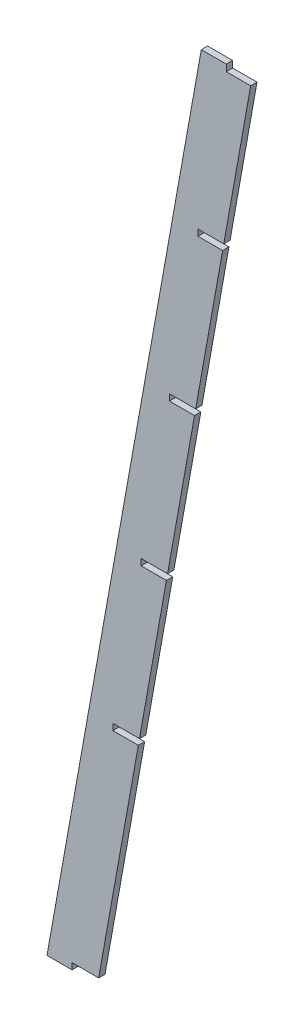
SolidWorks part; units mm, degrees
material "Plywood"
ref_plane "Front Plane" through (0, 0, 0) normal (0, 0, 1) x (1, 0, 0)
ref_plane "Top Plane" through (0, 0, 0) normal (0, 1, 0) x (1, 0, 0)
ref_plane "Right Plane" through (0, 0, 0) normal (1, 0, 0) x (0, 0, -1)
sketch "Sketch1" plane through (0, 0, 0) normal (0, 1, 0) x (1, 0, 0)
  line L1 (0, 0) -> (25.4, 0)
  line L2 (0, 0) -> (0, 3.175)
  line L3 (0, 3.175) -> (25.4, 3.175)
  line L4 (25.4, 0) -> (25.4, 3.175)
  dimension "D1" = 25.4
  dimension "D2" = 3.175
ref_plane "Plane1" through (0, 432.562, 0) normal (0, 1, 0) x (1, 0, 0)
sketch "Sketch2" plane through (0, 432.562, 0) normal (0, 1, 0) x (1, 0, 0)
  line L1 (77.47, 0) -> (102.87, 0)
  line L2 (77.47, 0) -> (77.47, 3.175)
  line L3 (77.47, 3.175) -> (102.87, 3.175)
  line L4 (102.87, 0) -> (102.87, 3.175)
  dimension "D1" = 25.4
  dimension "D2" = 3.175
  dimension "D3" = 0
  dimension "D4" = 77.47
loft "Loft1" add profiles "Sketch1", "Sketch2"
sketch "Sketch3" plane through (0, 0, 0) normal (0, 0, 1) x (1, 0, 0)
  line L0 (90.0287, 432.562) -> (90.0287, 429.26)
  line L9 (12.5729, 3.175) -> (12.5729, 0)
  line L11 (102.2786, 429.26) -> (90.0287, 429.26)
  line L12 (25.4, 0) -> (102.87, 432.562) construction
  line L13 (90.0287, 432.562) -> (102.87, 432.562)
  line L14 (102.87, 432.562) -> (102.2786, 429.26)
  line L15 (33.0714, 117.475) -> (33.0714, 114.3)
  line L16 (75.7597, 353.7381) -> (75.7597, 350.5952)
  line L17 (75.7597, 353.7381) -> (88.753, 353.7381)
  line L18 (75.7597, 350.5952) -> (88.1901, 350.5952)
  line L19 (88.1901, 350.5952) -> (88.753, 353.7381)
  line L20 (61.4709, 274.955) -> (61.4709, 271.78)
  line L21 (47.2604, 193.04) -> (47.2604, 196.215)
  line L22 (61.4709, 271.78) -> (74.0746, 271.78)
  line L23 (74.0746, 271.78) -> (74.6433, 274.955)
  line L24 (74.6433, 274.955) -> (61.4709, 274.955)
  line L25 (60.5413, 196.215) -> (59.9726, 193.04)
  line L26 (59.9726, 193.04) -> (47.2604, 193.04)
  line L27 (47.2604, 196.215) -> (60.5413, 196.215)
  line L28 (45.8706, 114.3) -> (46.4393, 117.475)
  line L29 (46.4393, 117.475) -> (33.0714, 117.475)
  line L30 (33.0714, 114.3) -> (45.8706, 114.3)
  line L31 (12.5729, 0) -> (25.4, 0)
  line L32 (25.4, 0) -> (25.9686, 3.175)
  line L33 (25.9686, 3.175) -> (12.5729, 3.175)
extrude "Cut-Extrude1" cut sketch "Sketch3" against normal blind 5.08
